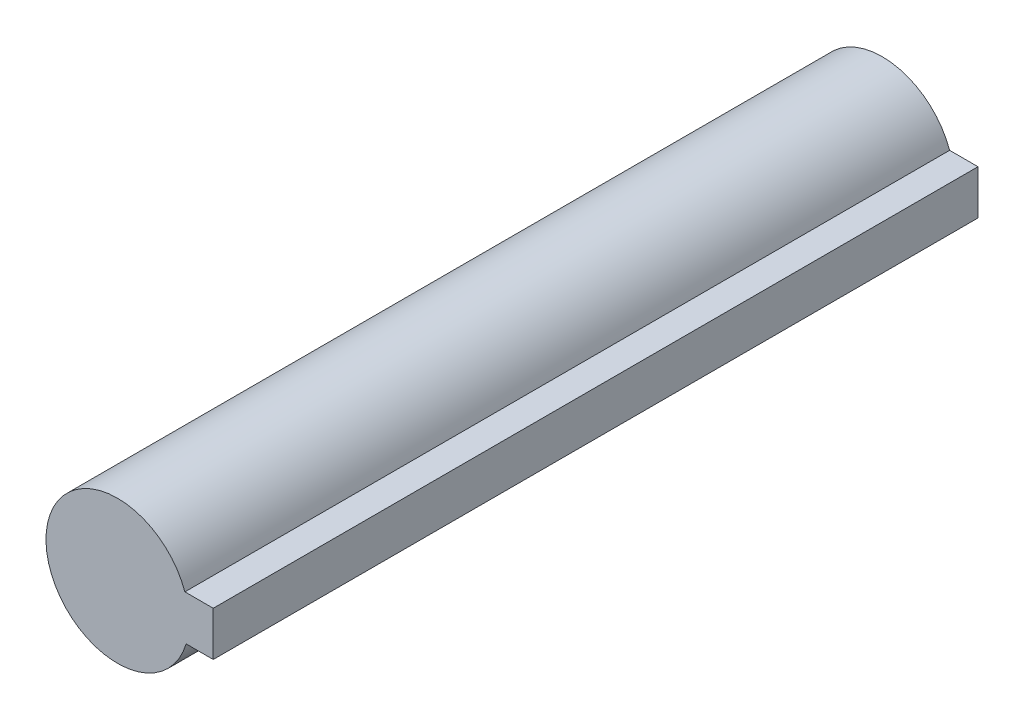
SolidWorks part; units mm, degrees
ref_plane "Front Plane" through (0, 0, 0) normal (1, 0, 0) x (0, 1, 0)
ref_plane "Top Plane" through (0, 0, 0) normal (0, 0, 1) x (0, 1, 0)
ref_plane "Right Plane" through (0, 0, 0) normal (0, 1, 0) x (-1, 0, 0)
sketch "Sketch1" plane through (0, 0, 0) normal (0, 0, 1) x (0, 1, 0)
  line L2 (-0.8235, -2.7806) -> (-0.8235, -3.8806)
  line L3 (-0.8235, -3.8806) -> (0.9765, -3.8806)
  line L4 (0.9765, -2.7306) -> (0.9765, -3.8806)
  arc A0 (0.9765, -2.7306) -> (-0.8235, -2.7806) centre (0, 0) ccw
  dimension "D1" = 5.8
  dimension "D2" = 1.8
  dimension "D3" = 1.15
  dimension "D4" = 1.1
extrude "Boss-Extrude1" add sketch "Sketch1" along normal blind 31
